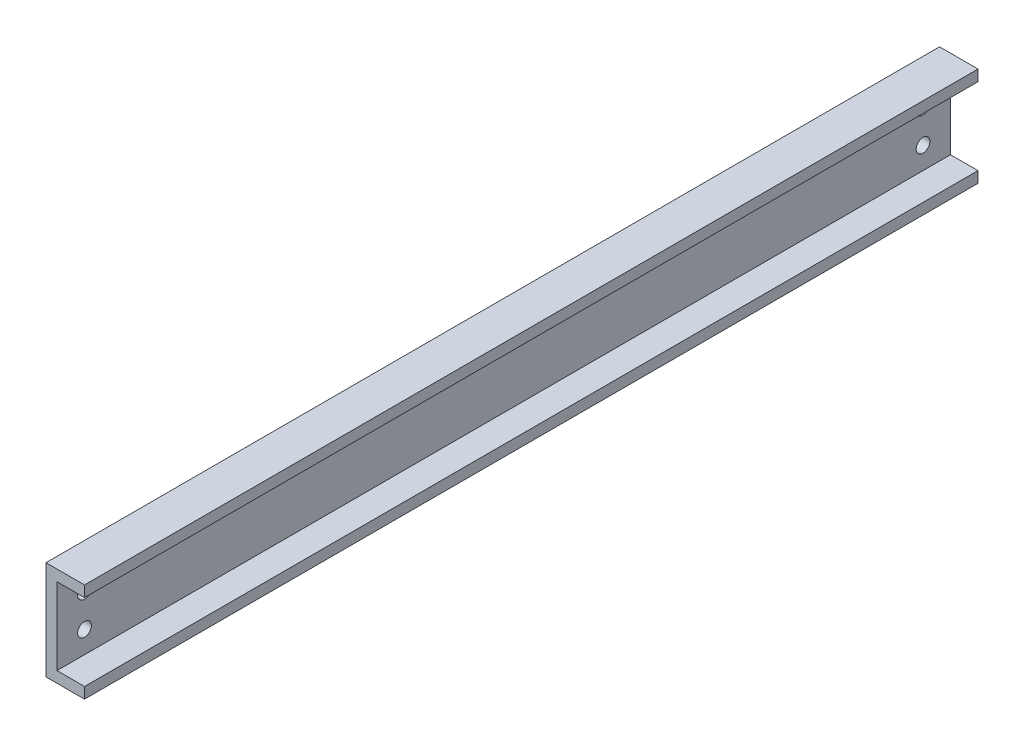
SolidWorks part; units mm, degrees
ref_plane "Front Plane" through (0, 0, 0) normal (0, 0, 1) x (1, 0, 0)
ref_plane "Top Plane" through (0, 0, 0) normal (0, 1, 0) x (1, 0, 0)
ref_plane "Right Plane" through (0, 0, 0) normal (1, 0, 0) x (0, 0, -1)
sketch "Sketch1" plane through (0, 0, 0) normal (0, 0, 1) x (1, 0, 0)
  line L0 (0, 9) -> (0, -9)
  line L1 (0, -9) -> (7, -9)
  line L2 (0, 9) -> (7, 9)
  line L3 (2, -7) -> (7, -7)
  line L4 (2, 7) -> (2, -7)
  line L5 (2, 7) -> (7, 7)
  line L6 (7, -9) -> (7, -7)
  line L7 (7, 9) -> (7, 7)
  dimension "D1" = 18
  dimension "D2" = 9
  dimension "D3" = 7
  dimension "D4" = 7
  dimension "D5" = 2
extrude "Boss-Extrude1" add sketch "Sketch1" against normal blind 162.5
sketch "Sketch2" plane through (0, 0, 0) normal (-1, 0, 0) x (0, 0, 1)
  line L0 (-2, 9) -> (-2, -9) construction
  line L1 (-162.5, 9) -> (0, 9) construction
  line L2 (-162.5, -9) -> (0, -9) construction
  line L3 (0, 9) -> (0, -9) construction
  line L4 (0, 0) -> (-162.5, 0) construction
  line L5 (-162.5, 9) -> (-162.5, -9) construction
  line L6 (-81.25, 9) -> (-81.25, -9) construction
  circle A0 centre (-5, 3) radius 1.25
  circle A2 centre (-5, -3) radius 1.25
  circle A3 centre (-157.5, -3) radius 1.25
  circle A4 centre (-157.5, 3) radius 1.25
  point P25 (2.1263, -3.3467)
  dimension "D2" = 2.5
  dimension "D1" = 2
  dimension "D3" = 3
  dimension "D4" = 3
extrude "Cut-Extrude1" cut sketch "Sketch2" against normal through all
